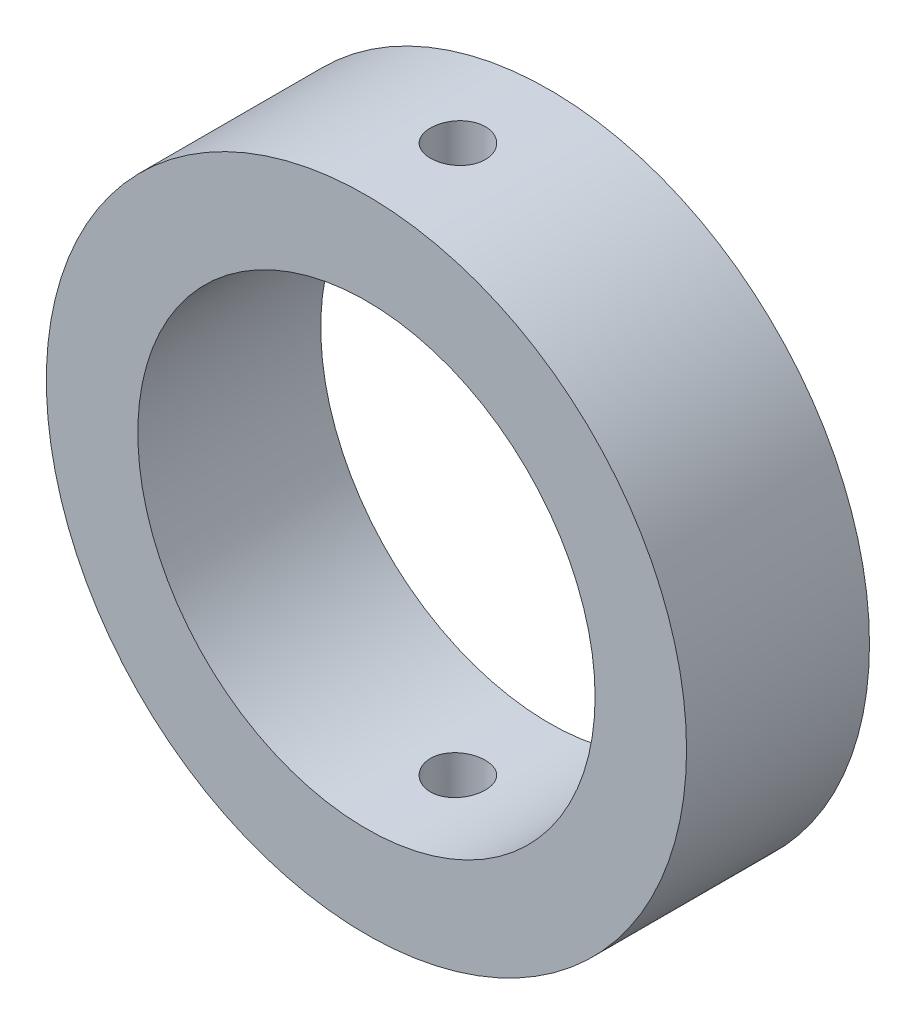
SolidWorks part; units mm, degrees
ref_plane "Front Plane" through (0, 0, 0) normal (0, 0, 1) x (1, 0, 0)
ref_plane "Top Plane" through (0, 0, 0) normal (0, 1, 0) x (1, 0, 0)
ref_plane "Right Plane" through (0, 0, 0) normal (1, 0, 0) x (0, 0, -1)
sketch "Sketch1" plane through (0, 0, 0) normal (0, 0, 1) x (1, 0, 0)
  circle A0 centre (0, 0) radius 250
  circle A1 centre (0, 0) radius 350
  dimension "D1" = 500
  dimension "D2" = 700
extrude "Boss-Extrude1" add sketch "Sketch1" along normal blind 200
sketch "Sketch2" plane through (0, 0, 0) normal (0, 1, 0) x (1, 0, 0)
  line L0 (250, 0) -> (-250, 0) construction
  circle A0 centre (0, -100) radius 30
  point P4 (0, 0)
  dimension "D1" = 60
  dimension "D2" = 100
extrude "Cut-Extrude1" cut sketch "Sketch2" against normal through all both and the other way through all
